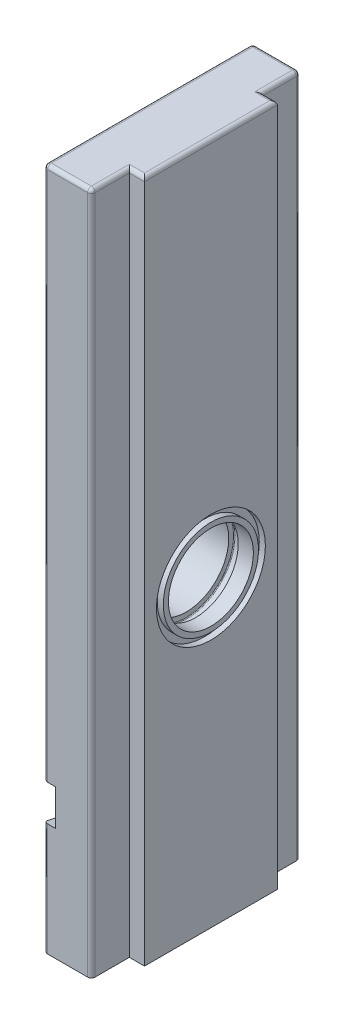
SolidWorks part; units mm, degrees
material "Perspex (TM) GS Acrylic Cast Sheet"
ref_plane "Front Plane" through (0, 0, 0) normal (0, 0, 1) x (1, 0, 0)
ref_plane "Top Plane" through (0, 0, 0) normal (0, 1, 0) x (1, 0, 0)
ref_plane "Right Plane" through (0, 0, 0) normal (1, 0, 0) x (0, 0, -1)
sketch "Sketch1" plane through (0, 0, 0) normal (0, 1, 0) x (1, 0, 0)
  line L0 (0, 0) -> (0, 55)
  line L1 (0, 55) -> (12.5, 55)
  line L2 (12.5, 55) -> (12.5, 45)
  line L3 (12.5, 45) -> (16.5, 45)
  line L4 (16.5, 45) -> (16.5, 10)
  line L5 (16.5, 10) -> (12.5, 10)
  line L6 (12.5, 10) -> (12.5, 0)
  line L7 (12.5, 0) -> (0, 0)
  line L8 (12.5, 45) -> (12.5, 10) construction
  dimension "D1" = 12.5
  dimension "D2" = 55
  dimension "D3" = 4
  dimension "D4" = 10
  dimension "D5" = 10
extrude "Boss-Extrude1" add sketch "Sketch1" along normal blind 180
sketch "Sketch3" plane through (16.5, 0, 0) normal (1, 0, 0) x (0, 0, -1)
  line L0 (10, 180) -> (45, 180) construction
  line L1 (27.5, 180) -> (27.5, 80.9914) construction
  circle A0 centre (27.5, 80) radius 11.2
  dimension "D1" = 100
  dimension "D3" = 22.4
extrude "Cut-Extrude1" cut sketch "Sketch3" against normal through all
ref_point "Point1"
ref_axis "Axis1" through (16.5, 80, -27.5) along (-1, 0, 0)
ref_plane "Plane1" through (0, 0, -27.5) normal (0, 0, 1) x (1, 0, 0)
sketch "Sketch11" plane through (0, 0, -27.5) normal (0, 0, 1) x (1, 0, 0)
  line L0 (12.5, 180) -> (12.5, 0) construction
  line L1 (10, 69.15) -> (12.5, 69.15)
  line L2 (10, 69.15) -> (10, 67.55)
  line L3 (10.2, 67.35) -> (12.3, 67.35)
  line L4 (12.5, 69.15) -> (12.5, 67.55)
  line L5 (16.5, 80) -> (-45.611, 80) construction
  line L6 (16.5, 180) -> (16.5, 0) construction
  line L7 (14.9, 67.45) -> (16.5, 67.45)
  line L8 (14.9, 67.45) -> (14.9, 65.65)
  line L9 (14.9, 65.65) -> (16.5, 65.65)
  line L10 (16.5, 67.45) -> (16.5, 65.65)
  arc A0 (12.3, 67.35) -> (12.5, 67.55) centre (12.3, 67.55) ccw
  arc A1 (10, 67.55) -> (10.2, 67.35) centre (10.2, 67.55) ccw
  point P16 (12.5, 67.35)
  point P19 (10, 67.35)
  dimension "D7" = 0.2
  dimension "D1" = 12.65
  dimension "D2" = 1.8
  dimension "D3" = 2.5
  dimension "D4" = 1.8
  dimension "D5" = 1.6
  dimension "D6" = 12.55
revolve "Cut-Revolve1" cut sketch "Sketch11" angle 360 about axis through (16.5, 80, -27.5) along (-1, 0, 0)
sketch "Sketch12" plane through (16.5, 0, 0) normal (1, 0, 0) x (0, 0, -1)
  line L0 (27.5, 80) -> (27.5, 180) construction
  line L1 (10, 180) -> (45, 180) construction
pattern_linear "LPattern1" count 2 spacing 60 along (0, 1, 0) of "Cut-Extrude1", "Cut-Revolve1"
hole_wizard "M6 Tapped Hole1" positions "Sketch14" profile "Sketch13" tap size "M6" standard "ISO"
sketch "Sketch14" plane through (0, 0, 0) normal (0, -1, 0) x (1, 0, 0)
  line L0 (12.5, 0) -> (12.5, -10) construction
  line L2 (6.5, -12.5) -> (6.5, -42.5) construction
  line L13 (6.5, -27.5) -> (0, -27.5) construction
  line L14 (0, -55) -> (0, 0) construction
  point P0 (6.5, -12.5)
  point P1 (6.5, -42.5)
  dimension "D1" = 6
  dimension "D2" = 30
sketch "Sketch13" plane through (6.5, 0, -12.5) normal (1, 0, 0) x (0, 0, -1)
  line L0 (0, 0) -> (0, 28.5022)
  line L1 (0, 28.5022) -> (2.5, 27)
  line L2 (2.5, 27) -> (2.5, 0)
  line L5 (2.5, 0) -> (0, 0)
  line L10 (0, 28.5022) -> (-2.5, 27) construction
  line L11 (0, -6.35) -> (0, 107.95) construction
  dimension "Tap Drill Dia." = 5
  dimension "Tap Drill Depth" = 27
  dimension "Drill Angle" = 118
cosmetic thread "Hole Thread1" parameters "D1"=22, "D2"=6
cosmetic thread "Hole Thread2" parameters "D1"=22, "D2"=6
sketch "Sketch15" plane through (0, 0, 0) normal (-1, 0, 0) x (0, 0, 1)
  line L0 (0, 180) -> (0, 0) construction
  line L1 (-55, 144.75) -> (-45.5, 146.75)
  line L2 (-55, 144.75) -> (-55, 135.25)
  line L3 (-55, 135.25) -> (-45.5, 133.25)
  line L4 (-45.5, 146.75) -> (-45.5, 133.25)
  line L5 (-27.5, 140) -> (-45.5, 140) construction
  line L6 (-55, 78.4) -> (-45.5, 80.4)
  line L7 (-45.5, 80.4) -> (-45.5, 66.9)
  line L8 (-45.5, 66.9) -> (-55, 68.9)
  line L9 (-55, 68.9) -> (-55, 78.4)
  line L10 (0, 39.2) -> (-9.5, 41.2)
  line L12 (-9.5, 41.2) -> (-9.5, 27.7)
  line L13 (-9.5, 27.7) -> (0, 29.7)
  line L14 (0, 29.7) -> (0, 39.2)
  line L15 (-27.5, 68.9) -> (-55, 68.9) construction
  line L16 (-27.5, 68.9) -> (-9.5, 68.9) construction
  line L17 (-9.5, 68.9) -> (-9.5, 41.2) construction
  line L18 (-9.5, 27.7) -> (-9.5, 0) construction
  line L19 (-55, 0) -> (0, 0) construction
  line L20 (-55, 180) -> (-55, 0) construction
  line L21 (-45.5, 140) -> (-55, 140) construction
  dimension "D1" = 9.5
  dimension "D2" = 13.5
  dimension "D3" = 9.5
extrude "Cut-Extrude2" cut sketch "Sketch15" against normal blind 3
fillet "Fillet1" radius 1 15 edges at (0, 180, -27.5) (6.25, 180, -55) (12.5, 180, -50) (14.5, 180, -45) (16.5, 180, -27.5) (14.5, 180, -10) (12.5, 180, -5) (6.25, 180, 0) (0, 14.85, 0) (12.5, 90, 0) (0, 109.6, 0) (0, 34.45, -55) (0, 106.825, -55) (0, 162.375, -55) (12.5, 90, -55)
sketch "Sketch16" plane through (16.5, 0, 0) normal (1, 0, 0) x (0, 0, -1)
  circle A0 centre (27.5, 140) radius 16.0862
extrude "Boss-Extrude2" add sketch "Sketch16" against normal up to surface (16.5 mm away) up to face at (0, 140, -38.7)
